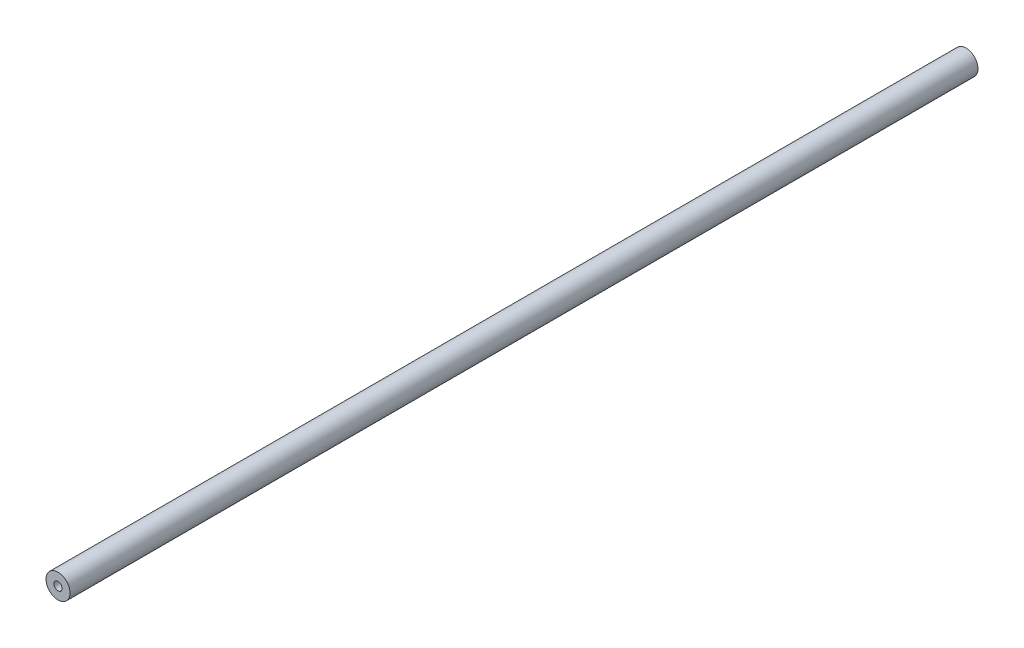
SolidWorks part; units mm, degrees
material "AISI 1020"
ref_plane "Спереди" through (0, 0, 0) normal (0, 0, 1) x (1, 0, 0)
ref_plane "Сверху" through (0, 0, 0) normal (0, 1, 0) x (1, 0, 0)
ref_plane "Справа" through (0, 0, 0) normal (1, 0, 0) x (0, 0, -1)
sketch "Эскиз1" plane through (0, 0, 0) normal (0, 0, 1) x (1, 0, 0)
  circle A0 centre (0, 0) radius 12.5
  dimension "D1" = 25
extrude "Бобышка-Вытянуть1" add sketch "Эскиз1" along normal blind 10 and the other way up to surface (461.6 mm away)
hole_wizard "Отверстие обработанное метчиком M101" positions "Эскиз2" profile "Эскиз3" tap size "M10" standard "ISO"
sketch "Эскиз2" plane through (0, 0, 10) normal (0, 0, 1) x (1, 0, 0)
  point P0 (0, 0)
sketch "Эскиз3" plane through (0, 0, 10) normal (1, 0, 0) x (0, -1, 0)
  line L0 (0, 0) -> (0, 30.0537)
  line L1 (0, 30.0537) -> (4.25, 27.5)
  line L2 (4.25, 27.5) -> (4.25, 0)
  line L5 (4.25, 0) -> (0, 0)
  line L10 (0, 30.0537) -> (-4.25, 27.5) construction
  line L11 (0, -6.35) -> (0, 107.95) construction
  dimension "Диаметр сверла" = 8.5
  dimension "Глубина сверла" = 27.5
  dimension "Угол заточки сверла" = 118
cosmetic thread "Отверстие резьбы1" parameters "D1"=20, "D2"=10
mirror "Зеркальное отражение1" about plane through (-175.3466, 75, -461.6) normal (0, 0, 1) of bodies 104
